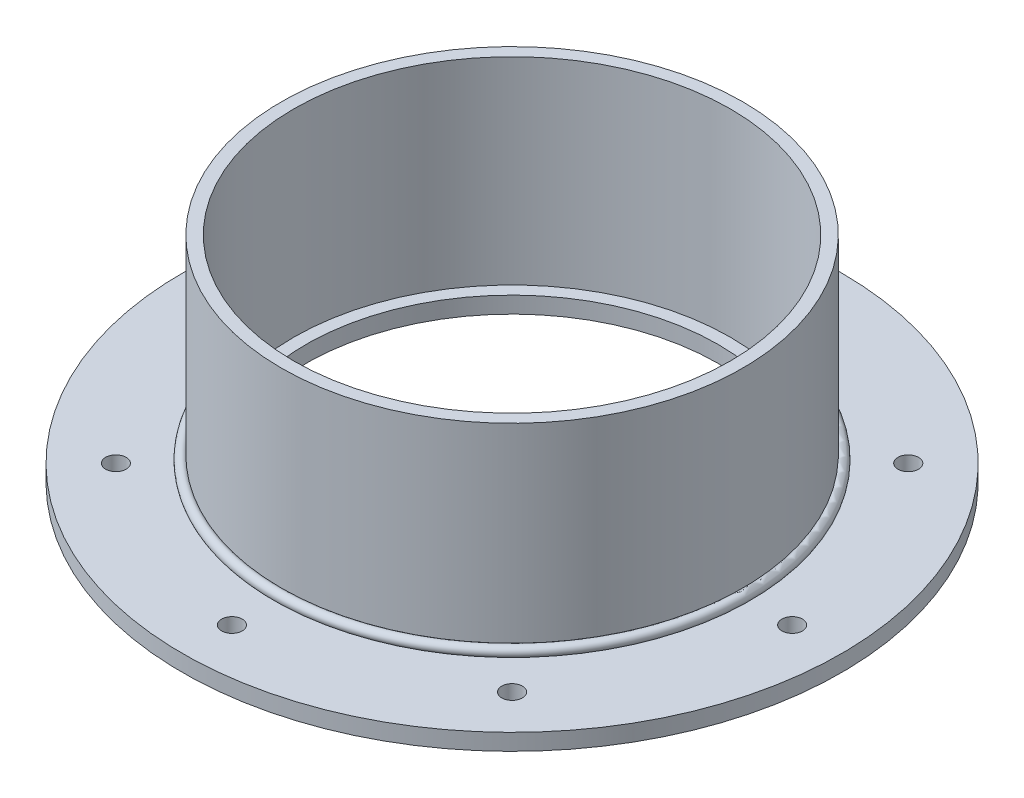
SolidWorks part; units mm, degrees
ref_plane "Front" through (0, 0, 0) normal (0, 0, 1) x (1, 0, 0)
ref_plane "Top" through (0, 0, 0) normal (0, 1, 0) x (1, 0, 0)
ref_plane "Right" through (0, 0, 0) normal (1, 0, 0) x (0, 0, -1)
sketch "Sketch1" plane through (0, 0, 0) normal (0, 0, 1) x (1, 0, 0)
  line L0 (0, 0) -> (0, 26.292) construction
  line L1 (-79.375, 0) -> (-127, 0)
  line L2 (-79.375, 0) -> (-79.375, 6.35)
  line L3 (-79.375, 6.35) -> (-127, 6.35)
  line L4 (-127, 0) -> (-127, 6.35)
  dimension "D1" = 6.35
  dimension "D2" = 254
  dimension "D3" = 158.75
revolve "Revolve1" add sketch "Sketch1" angle 360 about L0
sketch "Sketch2" plane through (0, 0, 0) normal (0, 0, 1) x (1, 0, 0)
  line L0 (127, 6.35) -> (-127, 6.35) construction
  line L1 (-88.9, 6.35) -> (-84.1375, 6.35)
  line L2 (-88.9, 6.35) -> (-88.9, 82.55)
  line L3 (-88.9, 82.55) -> (-84.1375, 82.55)
  line L4 (-84.1375, 6.35) -> (-84.1375, 82.55)
  line L5 (0, 0) -> (0, 56.4767) construction
  line L6 (-127, 0) -> (127, 0) construction
  dimension "D1" = 4.7625
  dimension "D2" = 168.275
  dimension "D3" = 82.55
revolve "Revolve2" add sketch "Sketch2" angle 360 about L5
sketch "Sketch3" plane through (0, 0, 0) normal (0, 0, 1) x (1, 0, 0)
  line L0 (-90.1234, 7.5734) -> (-88.9, 6.35) construction
  line L1 (127, 6.35) -> (-127, 6.35) construction
  line L2 (-88.9, 6.35) -> (-91.6858, 6.35)
  line L3 (-88.9, 82.55) -> (-88.9, 6.35) construction
  line L4 (-88.9, 9.1358) -> (-88.9, 6.35)
  line L5 (0, 0) -> (0, 19.0297) construction
  arc A0 (-88.9, 9.1358) -> (-91.6858, 6.35) centre (-90.1234, 7.5734) ccw
  dimension "D1" = 3.9688
  dimension "D2" = 45
  dimension "D3" = 2.7858
revolve "Revolve3" add sketch "Sketch3" angle 360 about L5
sketch "Sketch4" plane through (0, 6.35, 0) normal (0, 1, 0) x (1, 0, 0)
  circle A0 centre (0, 107.95) radius 3.9687
  circle A1 centre (0, 0) radius 107.95 construction
  dimension "D1" = 215.9
  dimension "D2" = 7.9375
extrude "Cut-Extrude1" cut sketch "Sketch4" against normal through all
pattern_circular "CirPattern1" count 8 over 360 about axis through (0, 0, 0) along (0, 1, 0) of "Cut-Extrude1"
